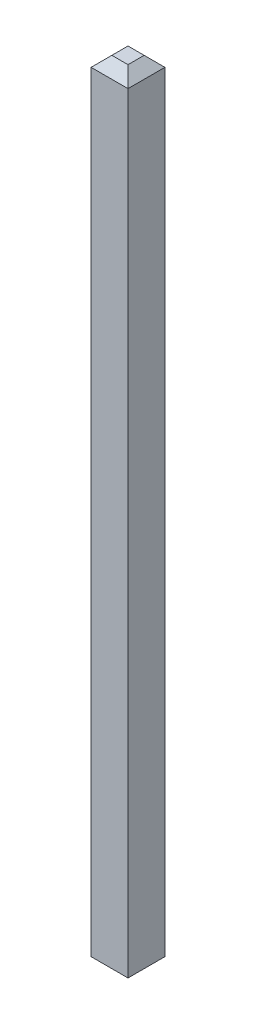
SolidWorks part; units mm, degrees
ref_plane "Plan de face" through (0, 0, 0) normal (0, 0, 1) x (1, 0, 0)
ref_plane "Plan de dessus" through (0, 0, 0) normal (0, 1, 0) x (1, 0, 0)
ref_plane "Plan de droite" through (0, 0, 0) normal (1, 0, 0) x (0, 0, -1)
sketch "Esquisse1" plane through (0, 0, 0) normal (0, 0, 1) x (1, 0, 0)
  line L0 (0, 1.2724) -> (0, -0.3329) construction
  line L2 (-0.1778, 0) -> (0.1778, 0)
  line L3 (-0.1778, 0) -> (-0.1778, 7.62)
  line L4 (-0.1778, 7.62) -> (0.1778, 7.62)
  line L5 (0.1778, 0) -> (0.1778, 7.62)
  dimension "D1" = 0.3556
  dimension "D2" = 7.62
extrude "Boss.-Extru.1" add sketch "Esquisse1" along normal blind 0.3556
chamfer "Chanfrein1" distance 0.1 angle 45 8 edges at (-0.1778, 7.62, 0.1778) (0, 7.62, 0) (0.1778, 7.62, 0.1778) (0, 7.62, 0.3556) (-0.1778, 0, 0.1778) (0, 0, 0) (0.1778, 0, 0.1778) (0, 0, 0.3556)
